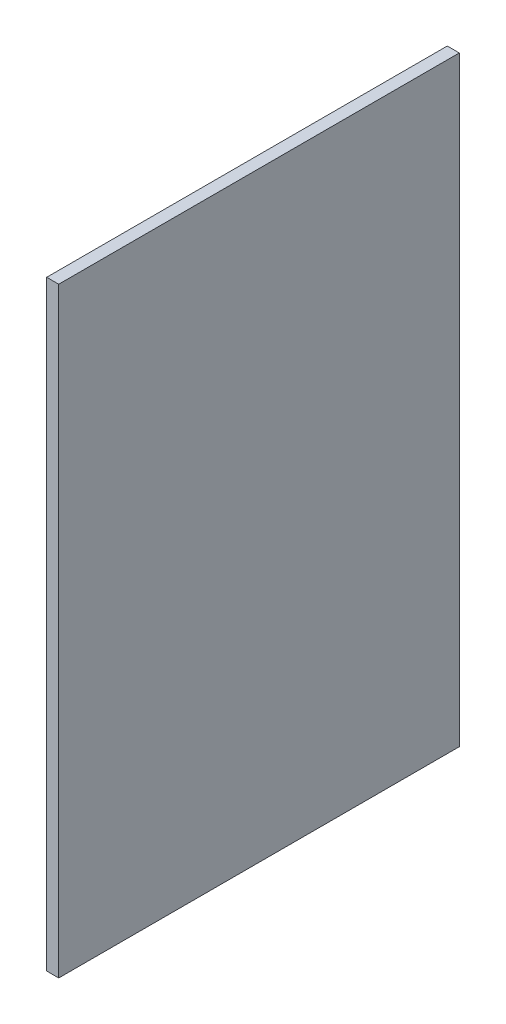
SolidWorks part; units mm, degrees
ref_plane "Спереди" through (0, 0, 0) normal (0, 0, 1) x (1, 0, 0)
ref_plane "Сверху" through (0, 0, 0) normal (0, 1, 0) x (1, 0, 0)
ref_plane "Справа" through (0, 0, 0) normal (1, 0, 0) x (0, 0, -1)
sketch "Эскиз1" plane through (0, 0, 0) normal (1, 0, 0) x (0, 0, -1)
  line L5 (0, 0) -> (600, 0)
  line L6 (0, 0) -> (0, 900)
  line L7 (0, 900) -> (600, 900)
  line L8 (600, 0) -> (600, 900)
extrude "Бобышка-Вытянуть1" add sketch "Эскиз1" along normal blind 18
